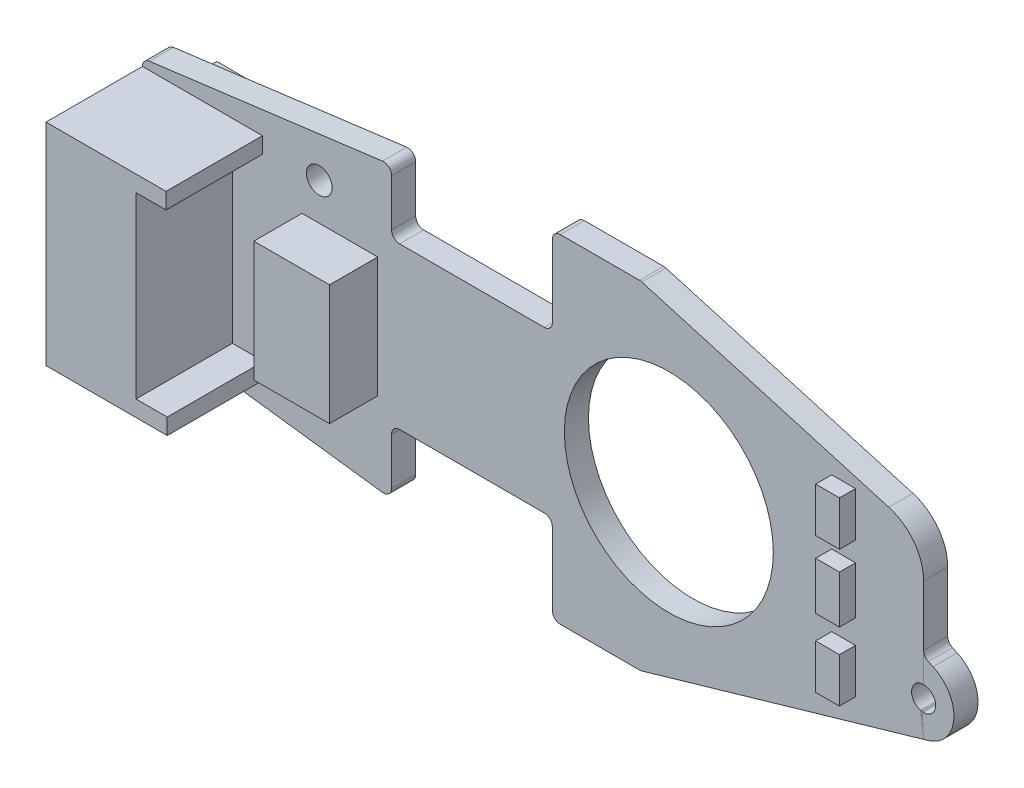
SolidWorks part; units mm, degrees
ref_plane "Plan de face" through (0, 0, 0) normal (0, 0, 1) x (1, 0, 0)
ref_plane "Plan de dessus" through (0, 0, 0) normal (0, 1, 0) x (1, 0, 0)
ref_plane "Plan de droite" through (0, 0, 0) normal (1, 0, 0) x (0, 0, -1)
sketch "Esquisse1" plane through (0, 0, 0) normal (0, 0, 1) x (1, 0, 0)
  line L0 (0, 0) -> (0, 6.5604)
  line L1 (0.436, 7.0563) -> (14.936, 8.9272)
  line L2 (15.5, 8.4313) -> (15.5, 5.5)
  line L3 (16, 5) -> (25, 5)
  line L4 (25.5, 5.5) -> (25.5, 10)
  line L5 (26, 10.5) -> (30.929, 10.5)
  line L6 (31.0682, 10.4802) -> (48.6, 5.4)
  line L7 (48.6, 5.4) -> (48.6, 0)
  line L8 (48.6, 0) -> (39.25, 0)
  line L9 (26.25, 0) -> (0, 0)
  arc A0 (0.436, 7.0563) -> (0, 6.5604) centre (0.5, 6.5604) ccw
  arc A1 (14.936, 8.9272) -> (15.5, 8.4313) centre (15, 8.4313) cw
  arc A2 (16, 5) -> (15.5, 5.5) centre (16, 5.5) cw
  arc A3 (25.5, 5.5) -> (25, 5) centre (25, 5.5) cw
  arc A4 (25.5, 10) -> (26, 10.5) centre (26, 10) cw
  arc A5 (30.929, 10.5) -> (31.0682, 10.4802) centre (30.929, 10) cw
  arc A6 (39.25, 0) -> (26.25, 0) centre (32.75, 0) ccw
  circle A7 centre (11, 5.92) radius 0.8
  point P12 (0, 7)
  point P15 (15.5, 9)
  point P18 (15.5, 5)
  point P21 (25.5, 5)
  point P24 (25.5, 10.5)
  point P27 (31, 10.5)
  dimension "D10" = 0.5
  dimension "D11" = 13
  dimension "D13" = 1.6
  dimension "D1" = 15.5
  dimension "D2" = 10
  dimension "D3" = 5.5
  dimension "D4" = 23.1
  dimension "D5" = 5.4
  dimension "D6" = 10.5
  dimension "D7" = 5
  dimension "D8" = 9
  dimension "D9" = 7
  dimension "D12" = 7.25
  dimension "D14" = 4.5
  dimension "D15" = 5.92
extrude "Extrusion1" add sketch "Esquisse1" along normal blind 1.5
mirror "Symétrie1" about plane through (0, 0, 0) normal (0, 1, 0) of bodies 101
sketch "Esquisse2" plane through (0, 0, 1.5) normal (0, 0, 1) x (1, 0, 0)
  line L0 (48.6, -5.4) -> (48.8999, -5.3131)
  line L2 (47.8453, -0.085) -> (48.6, -0.085)
  line L3 (47.8453, -0.085) -> (48.6, -5.4)
  line L4 (48.6, -5.4) -> (31.0682, -10.4802) construction
  line L6 (48.6, -5.4) -> (48.6, 5.4) construction
  line L7 (48.6, -0.085) -> (48.6, -0.6056)
  line L8 (48.8958, -1.062) -> (49.1861, -1.1918)
  arc A0 (48.8999, -5.3131) -> (49.1861, -1.1918) centre (48.2876, -3.2) ccw
  arc A1 (48.8958, -1.062) -> (48.6, -0.6056) centre (49.1, -0.6056) cw
  point P14 (48.6, -0.9296)
  dimension "D1" = 2.2
  dimension "D2" = 0.5
extrude "Extrusion2" add sketch "Esquisse2" against normal blind 1.5 separate body
fillet "Congé1" radius 3 1 edges at (48.6, 5.4, 0.75)
sketch "Esquisse3" plane through (0, 0, 1.5) normal (0, 0, 1) x (1, 0, 0)
  line L0 (48.6, -5.4) -> (48.6, 3.1459) construction
  circle A0 centre (48.6, -3.2) radius 0.75
  dimension "D1" = 1.5
  dimension "D2" = 2.2
extrude "Extrusion3" cut sketch "Esquisse3" against normal through all
sketch "Esquisse4" plane through (0, 0, 1.5) normal (0, 0, 1) x (1, 0, 0)
  line L0 (0, 6.5604) -> (7.4672, 6.5604)
  line L1 (7.4672, 6.5604) -> (7.4672, 5.5604)
  line L2 (7.4672, 5.5604) -> (5.5989, 5.5604)
  line L3 (5.5989, 5.5604) -> (5.5989, -5.5604)
  line L4 (5.5989, -5.5604) -> (7.5419, -5.5604)
  line L5 (7.5419, -5.5604) -> (7.5419, -6.5604)
  line L6 (7.5419, -6.5604) -> (0, -6.5604)
  line L7 (0, -6.5604) -> (0, 6.5604)
  arc A0 (0, -6.5604) -> (0.436, -7.0563) centre (0.5, -6.5604) ccw construction
  dimension "D1" = 1
  dimension "D2" = 1
extrude "Extrusion4" add sketch "Esquisse4" along normal blind 6
sketch "Esquisse5" plane through (0, 0, 1.5) normal (0, 0, 1) x (1, 0, 0)
  line L1 (9.9304, 3.6113) -> (14.638, 3.6113)
  line L2 (9.9304, 3.6113) -> (9.9304, -3.8692)
  line L3 (9.9304, -3.8692) -> (14.638, -3.8692)
  line L4 (14.638, 3.6113) -> (14.638, -3.8692)
extrude "Extrusion5" add sketch "Esquisse5" along normal blind 3
sketch "Esquisse6" plane through (0, 0, 1.5) normal (0, 0, 1) x (1, 0, 0)
  line L1 (42.8835, 5.9973) -> (44.3667, 5.9973)
  line L2 (42.8835, 5.9973) -> (42.8835, 3.2244)
  line L3 (42.8835, 3.2244) -> (44.3667, 3.2244)
  line L4 (44.3667, 5.9973) -> (44.3667, 3.2244)
  line L5 (42.8835, 1.9991) -> (44.3667, 1.9991)
  line L6 (42.8835, 1.9991) -> (42.8835, -0.9673)
  line L7 (42.8835, -0.9673) -> (44.3667, -0.9673)
  line L8 (44.3667, 1.9991) -> (44.3667, -0.9673)
  line L9 (42.8835, -2.4505) -> (44.3667, -2.4505)
  line L10 (42.8835, -2.4505) -> (42.8835, -5.2235)
  line L11 (42.8835, -5.2235) -> (44.3667, -5.2235)
  line L12 (44.3667, -2.4505) -> (44.3667, -5.2235)
extrude "Extrusion6" add sketch "Esquisse6" along normal blind 1
sketch "Esquisse7" plane through (0, 0, 0) normal (0, 0, -1) x (-1, 0, 0)
  line L1 (-2.1274, 6.6422) -> (-4.7714, 6.6422)
  line L2 (-2.1274, 6.6422) -> (-2.1274, 2.3215)
  line L3 (-2.1274, 2.3215) -> (-4.7714, 2.3215)
  line L4 (-4.7714, 6.6422) -> (-4.7714, 2.3215)
  line L5 (-2.1274, -6.5777) -> (-4.7714, -6.5777)
  line L6 (-2.1274, -6.5777) -> (-2.1274, -2.0636)
  line L7 (-2.1274, -2.0636) -> (-4.7714, -2.0636)
  line L8 (-4.7714, -6.5777) -> (-4.7714, -2.0636)
  line L9 (-15.6053, 3.1599) -> (-18.8297, 3.1599)
  line L10 (-15.6053, 3.1599) -> (-15.6053, -1.5477)
  line L11 (-15.6053, -1.5477) -> (-18.8297, -1.5477)
  line L12 (-18.8297, 3.1599) -> (-18.8297, -1.5477)
  line L13 (-46.7528, -2.0636) -> (-41.3358, -2.0636)
  line L14 (-46.7528, -2.0636) -> (-46.7528, 3.1599)
  line L15 (-46.7528, 3.1599) -> (-41.3358, 3.1599)
  line L16 (-41.3358, -2.0636) -> (-41.3358, 3.1599)
extrude "Extrusion7" add sketch "Esquisse7" along normal blind 1
sketch "Esquisse8" plane through (0, 0, 0) normal (-1, 0, 0) x (0, 0, 1)
  line L1 (2.3455, 5.7649) -> (6.8407, 5.7649)
  line L2 (2.3455, 5.7649) -> (2.3455, -5.8335)
  line L3 (2.3455, -5.8335) -> (6.8407, -5.8335)
  line L4 (6.8407, 5.7649) -> (6.8407, -5.8335)
extrude "Extrusion8" cut sketch "Esquisse8" against normal blind 4
